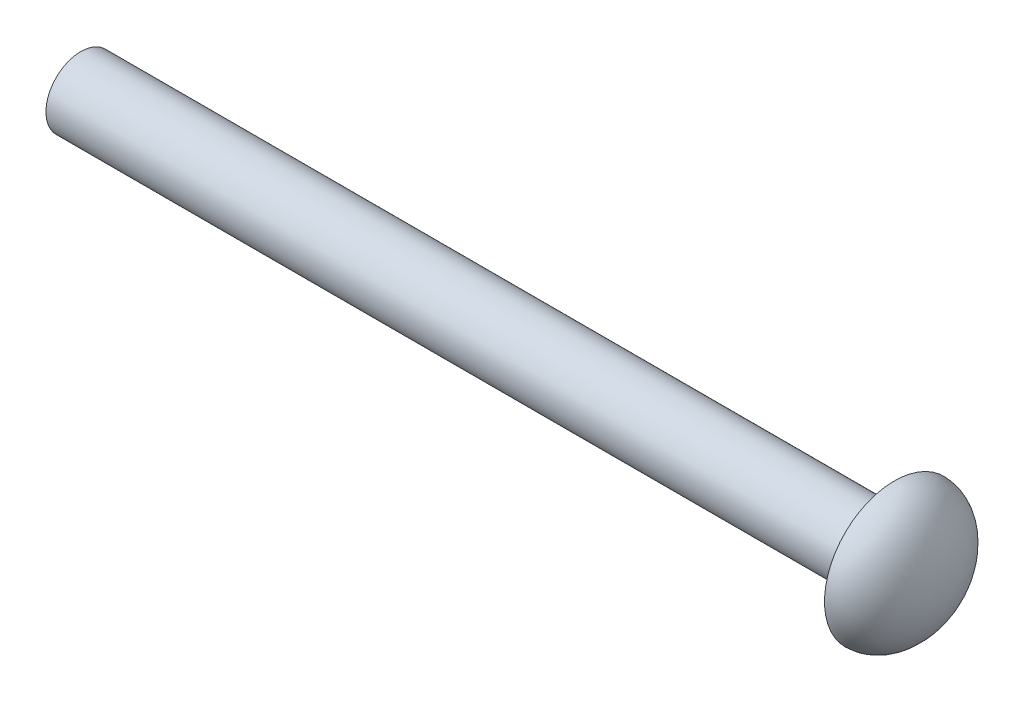
SolidWorks part; units mm, degrees
material "AISI 1020"
ref_plane "Front Plane" through (0, 0, 0) normal (0, 0, 1) x (1, 0, 0)
ref_plane "Top Plane" through (0, 0, 0) normal (0, 1, 0) x (1, 0, 0)
ref_plane "Right Plane" through (0, 0, 0) normal (1, 0, 0) x (0, 0, -1)
sketch "Sketch1" plane through (0, 0, 0) normal (1, 0, 0) x (0, 0, -1)
  circle A0 centre (0, 0) radius 1.5
  dimension "D1" = 3
extrude "Boss-Extrude1" add sketch "Sketch1" along normal blind 35
sketch "Sketch2" plane through (0, 0, 0) normal (0, 1, 0) x (1, 0, 0)
  line L4 (35, 0) -> (35, 3)
  line L5 (35, -1.5) -> (35, 1.5) construction
  line L6 (37, 0) -> (35, 0)
  ellipse E0 centre (35, 0) end of major axis (35, 3) minor radius 2 (37, 0) -> (35, 3) ccw
  point P6 (30, 4.0073)
  dimension "D1" = 2
  dimension "D2" = 3
revolve "Revolve1" add sketch "Sketch2" angle 360 about L6
